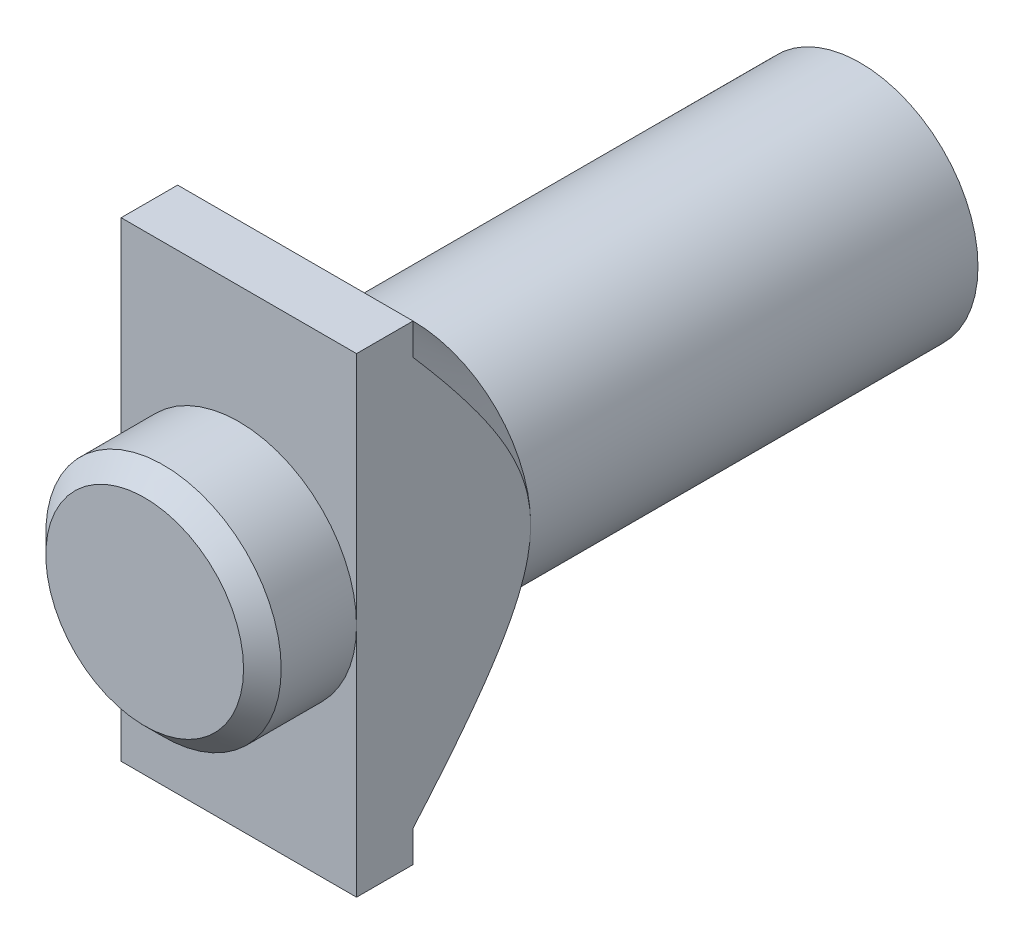
SolidWorks part; units mm, degrees
ref_plane "Front Plane" through (0, 0, 0) normal (0, 0, 1) x (1, 0, 0)
ref_plane "Top Plane" through (0, 0, 0) normal (0, 1, 0) x (1, 0, 0)
ref_plane "Right Plane" through (0, 0, 0) normal (1, 0, 0) x (0, 0, -1)
sketch "Sketch1" plane through (0, 0, 0) normal (0, 0, 1) x (1, 0, 0)
  circle A0 centre (0, 0) radius 6.25
  dimension "D1" = 12.5
extrude "Boss-Extrude1" add sketch "Sketch1" along normal blind 30
sketch "Sketch5" plane through (0, 0, 0) normal (1, 0, 0) x (0, 0, -1)
  line L0 (-63.5412, 0) -> (-78.0067, 0)
sketch "Sketch8" plane through (0, 0, 0) normal (0, 0, -1) x (-1, 0, 0)
  line L0 (-1.6163, 2.1) -> (1.6163, 2.1)
  arc A0 (-1.6163, 2.1) -> (1.6163, 2.1) centre (0, 0) ccw
  dimension "D1" = 5.3
  dimension "D2" = 2.1
extrude "Cut-Extrude3" cut sketch "Sketch8" against normal blind 15
sketch "Sketch9" plane through (0, 0, 30) normal (0, 0, 1) x (1, 0, 0)
  line L1 (6.25, 12.5) -> (-6.25, 12.5)
  line L2 (6.25, 12.5) -> (6.25, -12.5)
  line L3 (6.25, -12.5) -> (-6.25, -12.5)
  line L4 (-6.25, 12.5) -> (-6.25, -12.5)
  line L5 (6.25, 12.5) -> (-6.25, -12.5) construction
  line L6 (6.25, -12.5) -> (-6.25, 12.5) construction
  point P0 (0, 0)
  dimension "D1" = 12.5
  dimension "D2" = 25
extrude "Boss-Extrude2" add sketch "Sketch9" along normal blind 3
sketch "Sketch10" plane through (0, 0, 0) normal (1, 0, 0) x (0, 0, -1)
  line L0 (-30, 12.5) -> (-30, 0)
  line L1 (-30, 0) -> (-17.5, 0)
  line L2 (-17.5, 0) -> (-30, 12.5)
  dimension "D1" = 12.5
revolve "Revolve1" add sketch "Sketch10" angle 360 about L0
sketch "Sketch11" plane through (0, 0, 33) normal (0, 0, 1) x (1, 0, 0)
  line L0 (-6.25, 12.5) -> (-6.25, -12.5)
  line L1 (-6.25, -12.5) -> (-17.1838, -12.5)
  line L2 (-17.1838, -12.5) -> (-17.1838, 12.5)
  line L3 (-17.1838, 12.5) -> (-6.25, 12.5)
  line L4 (6.25, 12.5) -> (6.25, -12.5)
  line L5 (6.25, -12.5) -> (18.1887, -12.5)
  line L6 (18.1887, -12.5) -> (18.1887, 12.5)
  line L7 (18.1887, 12.5) -> (6.25, 12.5)
extrude "Cut-Extrude4" cut sketch "Sketch11" against normal through all
sketch "Sketch12" plane through (0, 0, 33) normal (0, 0, 1) x (1, 0, 0)
  circle A0 centre (0, 0) radius 6.25
extrude "Boss-Extrude3" add sketch "Sketch12" along normal blind 5
chamfer "Chamfer1" distance 1 angle 45 1 edges at (6.25, 0, 38)
